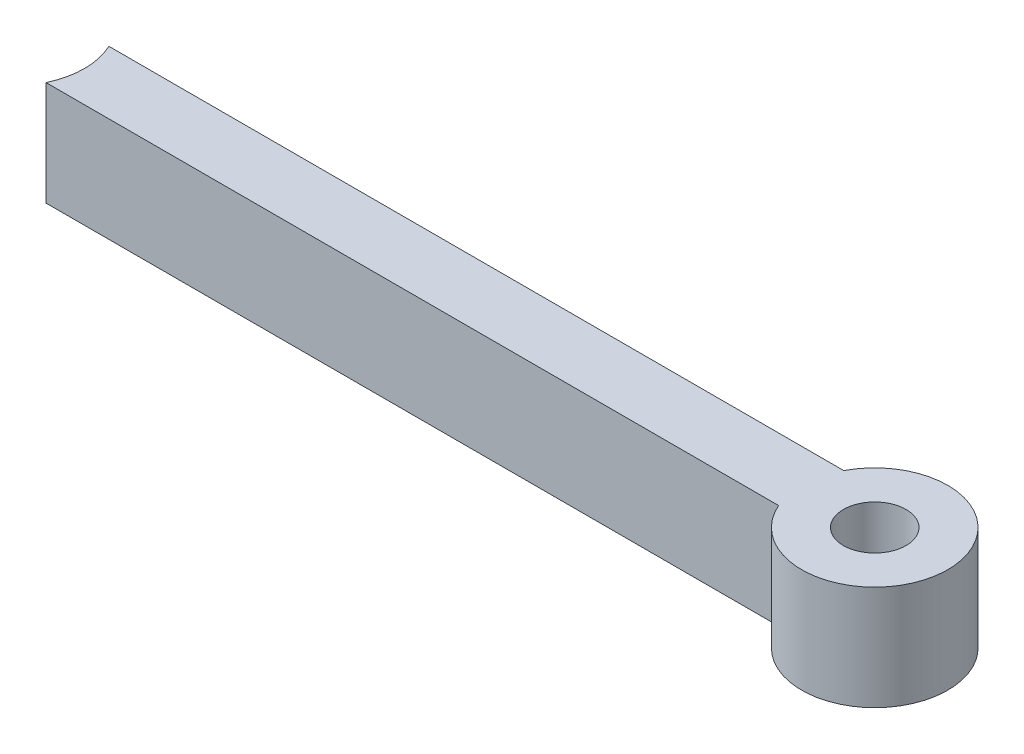
SolidWorks part; units mm, degrees
ref_plane "Plan de face" through (0, 0, 0) normal (0, 0, 1) x (1, 0, 0)
ref_plane "Plan de dessus" through (0, 0, 0) normal (0, 1, 0) x (1, 0, 0)
ref_plane "Plan de droite" through (0, 0, 0) normal (1, 0, 0) x (0, 0, -1)
sketch "Esquisse1" plane through (0, 0, 0) normal (0, 1, 0) x (1, 0, 0)
  line L0 (-327.7049, 30.0955) -> (379.4018, 30.0955)
  line L1 (-327.7049, -30.0955) -> (377.2097, -30.0955)
  line L2 (-327.7049, 30.0955) -> (-327.7049, -30.0955)
  circle A2 centre (441.4546, -2.2999) radius 70
  dimension "D1" = 707.1068
extrude "Boss.-Extru.2" add sketch "Esquisse1" along normal blind 100
sketch "Esquisse5" plane through (0, 100, 0) normal (0, 1, 0) x (1, 0, 0)
  circle A0 centre (441.4546, -2.2999) radius 30
extrude "Enlèv. mat.-Extru.4" cut sketch "Esquisse5" against normal through all
sketch "Esquisse6" plane through (0, 100, 0) normal (0, 1, 0) x (1, 0, 0)
  circle A0 centre (-387.7298, 0) radius 70
  point P3 (0, 0)
  point P4 (0, 0)
  point P5 (-389.2985, 0)
  point P6 (-387.7298, 0)
  point P7 (0, 0)
  point P8 (0, 0)
  point P9 (0, 0)
extrude "Enlèv. mat.-Extru.5" cut sketch "Esquisse6" against normal through all contours A0
equation "\"D1@Esquisse1\"=sqr(2)/2"
